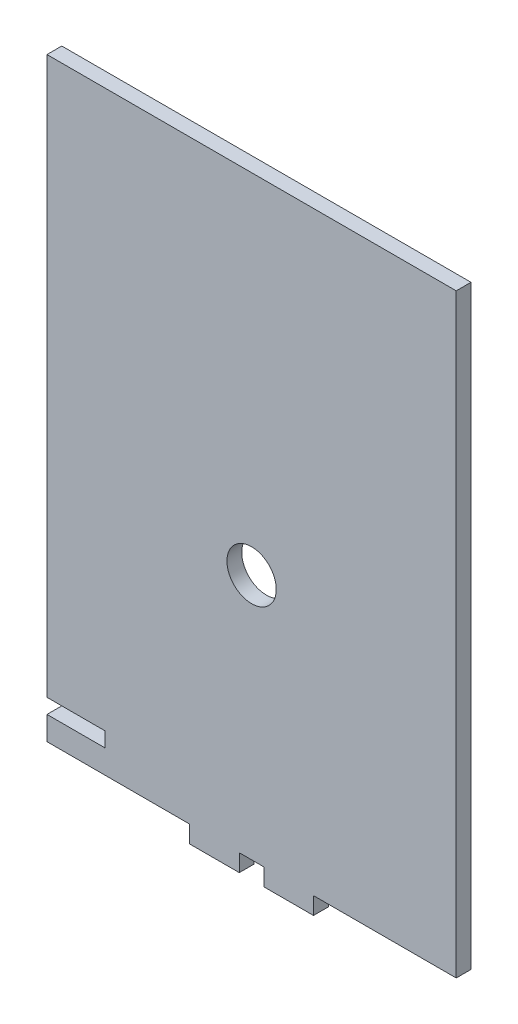
SolidWorks part; units mm, degrees
ref_plane "Alzado" through (0, 0, 0) normal (0, 0, 1) x (1, 0, 0)
ref_plane "Planta" through (0, 0, 0) normal (0, 1, 0) x (1, 0, 0)
ref_plane "Vista lateral" through (0, 0, 0) normal (1, 0, 0) x (0, 0, -1)
sketch "Model" plane through (0, 0, 0) normal (0, 0, 1) x (1, 0, 0)
  line L0 (68.9355, -35.8425) -> (68.9355, -32.349)
  line L1 (53.8855, -35.8425) -> (43.8355, -35.8425)
  line L2 (53.8855, -32.3425) -> (53.8855, -35.8425)
  line L3 (58.8855, -32.3425) -> (53.8855, -32.3425)
  line L4 (58.8855, -35.8425) -> (58.8855, -32.3425)
  line L5 (68.9355, -35.8425) -> (58.8855, -35.8425)
  line L6 (97.8855, -32.3471) -> (68.9355, -32.349)
  line L7 (97.8855, 88.3498) -> (97.8855, -32.3471)
  line L8 (14.8855, 88.3498) -> (97.8855, 88.3498)
  line L9 (14.8855, 88.3498) -> (14.8855, -5.5533)
  line L10 (26.6855, -24.5502) -> (14.8855, -24.5502)
  line L11 (26.6855, -27.5502) -> (26.6855, -24.5502)
  line L12 (14.8855, -27.5502) -> (26.6855, -27.5502)
  line L13 (14.8855, -24.5502) -> (14.8855, -5.5533)
  line L14 (26.6855, -24.5502) -> (14.8855, -24.5502)
  line L15 (14.8855, -32.3406) -> (14.8855, -27.5502)
  line L16 (43.8355, -32.349) -> (14.8855, -32.3406)
  line L17 (43.8355, -35.8425) -> (43.8355, -32.349)
  circle A0 centre (56.3855, 17.6498) radius 5
extrude "Saliente-Extruir1" add sketch "Model" along normal blind 3 contours L17 L1 L2 L3 L4 L5 L0 L6 L7 L8 L9 L13 L10 L11 L12 L15 L16 A0
